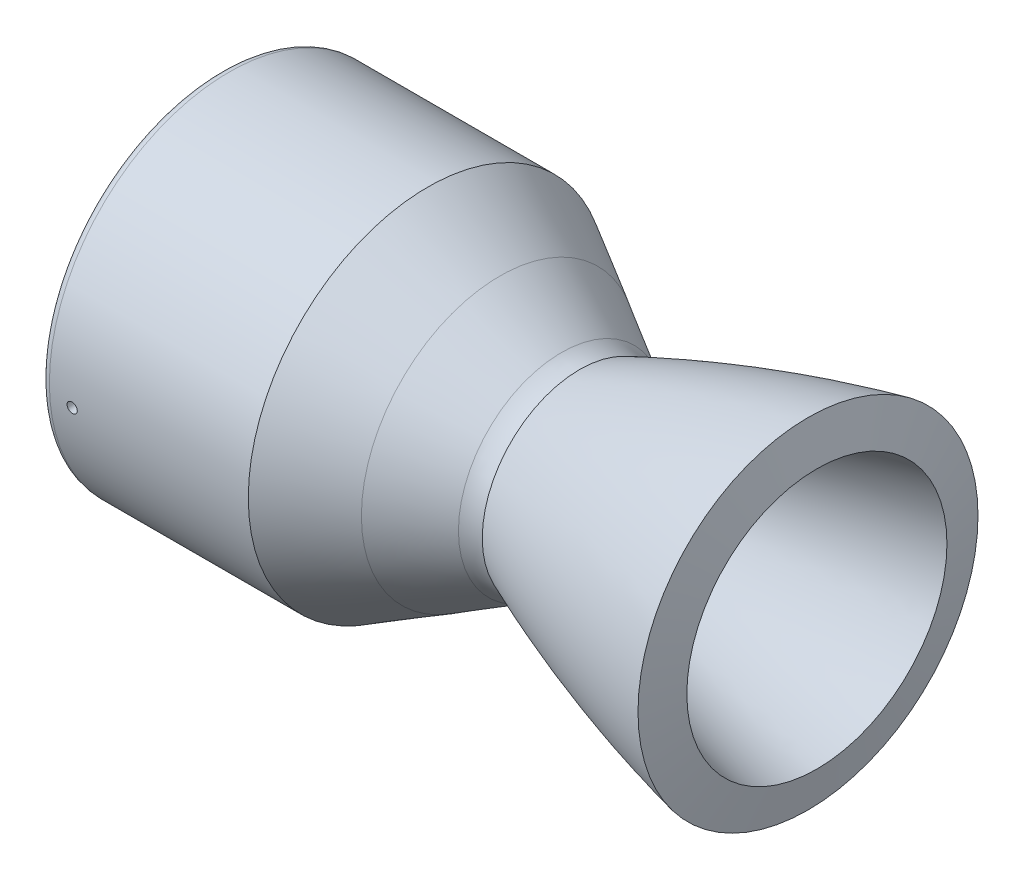
SolidWorks part; units mm, degrees
ref_plane "Front Plane" through (0, 0, 0) normal (0, 0, 1) x (1, 0, 0)
ref_plane "Top Plane" through (0, 0, 0) normal (0, 1, 0) x (1, 0, 0)
ref_plane "Right Plane" through (0, 0, 0) normal (1, 0, 0) x (0, 0, -1)
sketch "Model" plane through (0, 0, 0) normal (0, 0, 1) x (1, 0, 0)
  line L0 (-112.522, 43.0261) -> (-73.3839, 43.0261)
  line L1 (-32.2359, 32.0005) -> (-13.1434, 20.9774)
  line L2 (-0.0624, 17.4724) -> (-0.0499, 17.4724)
  line L3 (-112.522, 0) -> (72.4744, 0) construction
  line L4 (-112.522, 55.7261) -> (-48.2551, 55.7261)
  line L5 (-25.8859, 42.999) -> (-6.7934, 31.9759)
  line L6 (-1.1565, 30.2169) -> (-1.1565, 30.2169)
  line L7 (-112.522, 43.0261) -> (-112.522, 55.7261)
  line L8 (72.4744, 40.3605) -> (69.713, 52.7566)
  line L9 (-25.8859, 42.999) -> (-48.2551, 55.7261)
  line L10 (-112.522, 55.7261) -> (-73.3839, 55.7261) construction
  arc A0 (-0.0499, 17.4724) -> (2.5418, 17.9961) centre (-0.0499, 24.1468) ccw
  arc A1 (-0.0624, 17.4724) -> (-13.1434, 20.9774) centre (-0.0624, 43.6344) cw
  arc A2 (-32.2359, 32.0005) -> (-73.3839, 43.0261) centre (-73.3839, -39.2699) ccw
  arc A4 (-1.1565, 30.2169) -> (-6.7934, 31.9759) centre (-0.0624, 43.6344) cw
  arc A5 (-1.1565, 30.2169) -> (-1.1565, 30.2169) centre (-1.1565, 30.2169) ccw
  arc A7 (-25.8859, 42.999) -> (-73.3839, 55.7261) centre (-73.3839, -39.2699) ccw construction
  spline S0 degree 2 poles (2.5418, 17.9961) (36.7084, 32.393) (72.4744, 40.3605) knots 0 0 0 1 1 1
  spline S1 degree 1 poles (-1.1565, 30.2169) (69.713, 52.7566) knots 0 0 1 1 construction
  spline S2 degree 3 poles (-1.1565, 30.2169) (4.5961, 32.62) (16.2272, 37.1846) (39.705, 45.2264) (57.6343, 50.0659) (69.713, 52.7566) knots 0.017509 0.017509 0.017509 0.017509 0.263132 0.508754 1 1 1 1
  dimension "D1" = 26.162
  dimension "D2" = 82.296
  dimension "D4" = 30.2169
  dimension "D3" = 12.7
revolve "Revolve1" add sketch "Model" angle 360 about L3
fillet "Fillet1" radius 2.54 1 edges at (-112.522, 0, 55.7261)
ref_plane "Plane1" through (0, -3.1721, 55.6357) normal (0, -0.0569, 0.9984) x (-1, 0, 0)
sketch "Sketch2" plane through (0, -3.1721, 55.6357) normal (0, -0.0569, 0.9984) x (-1, 0, 0)
  circle A0 centre (102.997, 0) radius 1.5875
  dimension "D1" = 3.175
extrude "Cut-Extrude1" cut sketch "Sketch2" against normal up to next
ref_plane "Plane2" through (0, -55.6357, -3.1721) normal (0, -0.9984, -0.0569) x (-1, 0, 0)
sketch "Sketch3" plane through (0, -55.6357, -3.1721) normal (0, -0.9984, -0.0569) x (-1, 0, 0)
  circle A0 centre (106.172, 0) radius 5.207
  dimension "D1" = 10.414
extrude "Cut-Extrude2" cut sketch "Sketch3" against normal up to next
